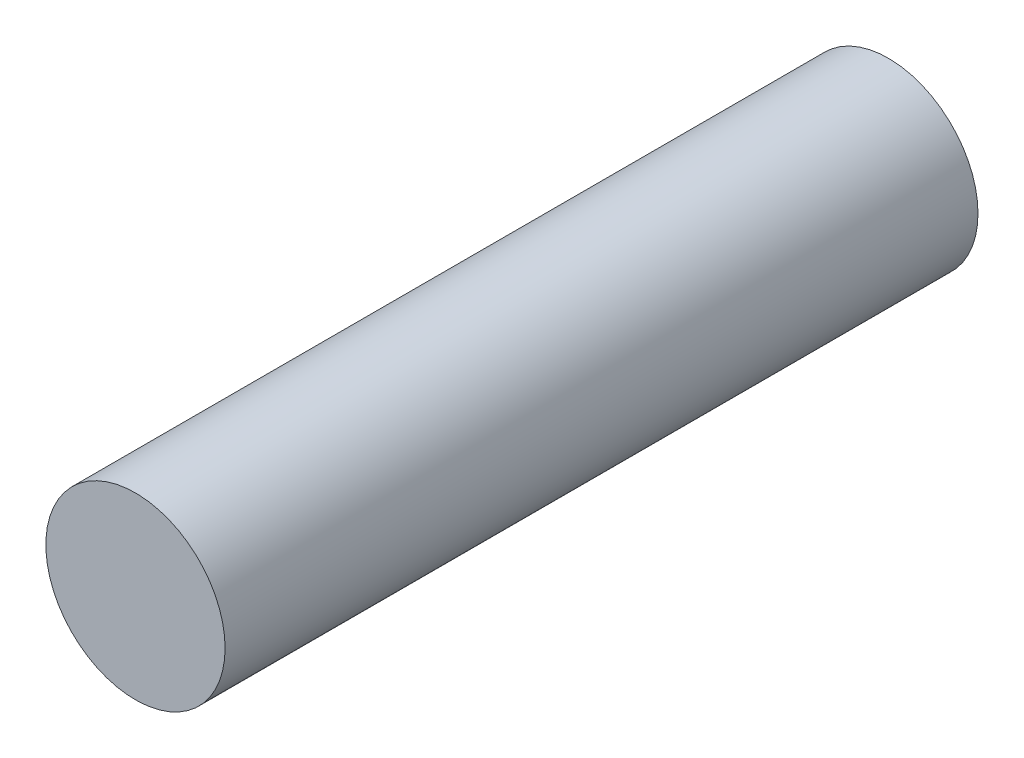
SolidWorks part; units mm, degrees
ref_plane "Plan1" through (0, 0, 0) normal (0, 0, 1) x (1, 0, 0)
ref_plane "Plan2" through (0, 0, 0) normal (0, 1, 0) x (1, 0, 0)
ref_plane "Plan3" through (0, 0, 0) normal (1, 0, 0) x (0, 0, -1)
sketch "Esquisse1" plane through (0, 0, 0) normal (0, 0, 1) x (1, 0, 0)
  circle A0 centre (0, 0) radius 0.5
  dimension "D1" = 1
extrude "Base-Extrusion" add sketch "Esquisse1" along normal mid plane 4.2
